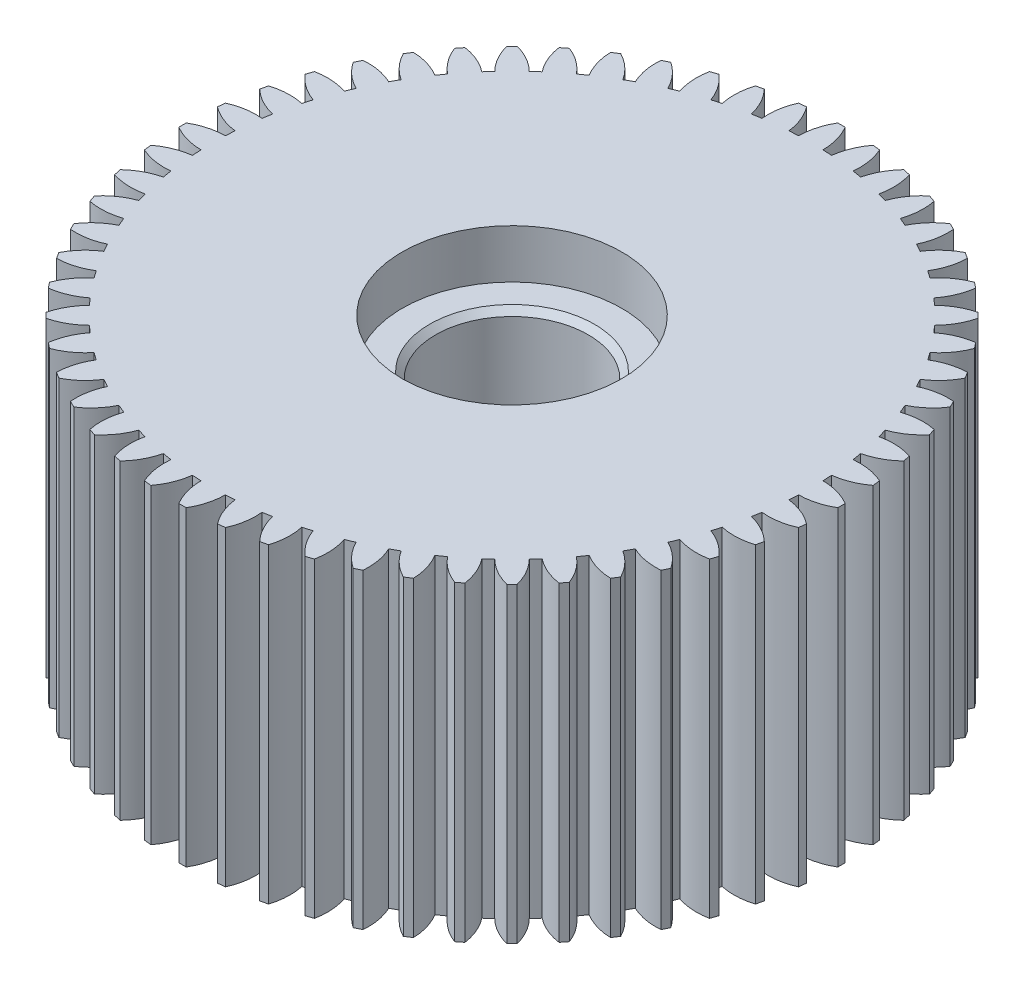
SolidWorks part; units mm, degrees
ref_plane "Front Plane" through (0, 0, 0) normal (0, 0, 1) x (1, 0, 0)
ref_plane "Top Plane" through (0, 0, 0) normal (0, 1, 0) x (1, 0, 0)
ref_plane "Right Plane" through (0, 0, 0) normal (1, 0, 0) x (0, 0, -1)
sketch "Sketch2" plane through (0, 0, 0) normal (0, 1, 0) x (1, 0, 0)
  circle A0 centre (0, 0) radius 24.5
  dimension "D1" = 49
extrude "Boss-Extrude1" add sketch "Sketch2" along normal blind 25.5
sketch "Sketch3" plane through (0, 25.5, 0) normal (0, 1, 0) x (1, 0, 0)
  line L0 (0, 0) -> (0, 40.3365) construction
  line L1 (-0.3, 26.9983) -> (0.3, 26.9983)
  line L2 (2.7247, 26.8622) -> (3.321, 26.795)
  line L3 (5.7152, 26.3882) -> (6.3002, 26.2547)
  line L4 (8.6338, 25.5824) -> (9.2001, 25.3842)
  line L5 (11.4438, 24.4548) -> (11.9844, 24.1945)
  line L6 (14.11, 23.0198) -> (14.618, 22.7005)
  line L7 (16.5986, 21.2952) -> (17.0677, 20.9211)
  line L8 (18.8786, 19.3028) -> (19.3028, 18.8786)
  line L9 (20.9211, 17.0677) -> (21.2952, 16.5986)
  line L10 (22.7005, 14.618) -> (23.0198, 14.11)
  line L11 (24.1945, 11.9844) -> (24.4548, 11.4438)
  line L12 (25.3842, 9.2001) -> (25.5824, 8.6338)
  line L13 (26.2547, 6.3002) -> (26.3882, 5.7152)
  line L14 (26.795, 3.321) -> (26.8622, 2.7247)
  line L15 (26.9983, 0.3) -> (26.9983, -0.3)
  line L16 (26.8622, -2.7247) -> (26.795, -3.321)
  line L17 (26.3882, -5.7152) -> (26.2547, -6.3002)
  line L18 (25.5824, -8.6338) -> (25.3842, -9.2001)
  line L19 (24.4548, -11.4438) -> (24.1945, -11.9844)
  line L20 (23.0198, -14.11) -> (22.7005, -14.618)
  line L21 (21.2952, -16.5986) -> (20.9211, -17.0677)
  line L22 (19.3028, -18.8786) -> (18.8786, -19.3028)
  line L23 (17.0677, -20.9211) -> (16.5986, -21.2952)
  line L24 (14.618, -22.7005) -> (14.11, -23.0198)
  line L25 (11.9844, -24.1945) -> (11.4438, -24.4548)
  line L26 (9.2001, -25.3842) -> (8.6338, -25.5824)
  line L27 (6.3002, -26.2547) -> (5.7152, -26.3882)
  line L28 (3.321, -26.795) -> (2.7247, -26.8622)
  line L29 (0.3, -26.9983) -> (-0.3, -26.9983)
  line L30 (-2.7247, -26.8622) -> (-3.321, -26.795)
  line L31 (-5.7152, -26.3882) -> (-6.3002, -26.2547)
  line L32 (-8.6338, -25.5824) -> (-9.2001, -25.3842)
  line L33 (-11.4438, -24.4548) -> (-11.9844, -24.1945)
  line L34 (-14.11, -23.0198) -> (-14.618, -22.7005)
  line L35 (-16.5986, -21.2952) -> (-17.0677, -20.9211)
  line L36 (-18.8786, -19.3028) -> (-19.3028, -18.8786)
  line L37 (-20.9211, -17.0677) -> (-21.2952, -16.5986)
  line L38 (-22.7005, -14.618) -> (-23.0198, -14.11)
  line L39 (-24.1945, -11.9844) -> (-24.4548, -11.4438)
  line L40 (-25.3842, -9.2001) -> (-25.5824, -8.6338)
  line L41 (-26.2547, -6.3002) -> (-26.3882, -5.7152)
  line L42 (-26.795, -3.321) -> (-26.8622, -2.7247)
  line L43 (-26.9983, -0.3) -> (-26.9983, 0.3)
  line L44 (-26.8622, 2.7247) -> (-26.795, 3.321)
  line L45 (-26.3882, 5.7152) -> (-26.2547, 6.3002)
  line L46 (-25.5824, 8.6338) -> (-25.3842, 9.2001)
  line L47 (-24.4548, 11.4438) -> (-24.1945, 11.9844)
  line L48 (-23.0198, 14.11) -> (-22.7005, 14.618)
  line L49 (-21.2952, 16.5986) -> (-20.9211, 17.0677)
  line L50 (-19.3028, 18.8786) -> (-18.8786, 19.3028)
  line L51 (-17.0677, 20.9211) -> (-16.5986, 21.2952)
  line L52 (-14.618, 22.7005) -> (-14.11, 23.0198)
  line L53 (-11.9844, 24.1945) -> (-11.4438, 24.4548)
  line L54 (-9.2001, 25.3842) -> (-8.6338, 25.5824)
  line L55 (-6.3002, 26.2547) -> (-5.7152, 26.3882)
  line L56 (-3.321, 26.795) -> (-2.7247, 26.8622)
  circle A0 centre (0, 0) radius 24.5 construction
  circle A1 centre (0, 0) radius 24.5
  circle A2 centre (0, 0) radius 27
  arc A3 (-1, 24.4796) -> (-0.3, 26.9983) centre (3.9999, 24.4467) cw
  arc A4 (1, 24.4796) -> (0.3, 26.9983) centre (-3.9999, 24.4467) ccw
  arc A5 (1.7471, 24.4376) -> (2.7247, 26.8622) centre (6.7119, 23.8451) cw
  arc A6 (3.7346, 24.2137) -> (3.321, 26.795) centre (-1.2376, 24.7408) ccw
  arc A7 (4.4723, 24.0884) -> (5.7152, 26.3882) centre (9.3395, 22.9437) cw
  arc A8 (6.4221, 23.6433) -> (6.3002, 26.2547) centre (1.5403, 24.7238) ccw
  arc A9 (7.1412, 23.4361) -> (8.6338, 25.5824) centre (11.8497, 21.7537) cw
  arc A10 (9.029, 22.7756) -> (9.2001, 25.3842) centre (4.2988, 24.3959) ccw
  arc A11 (9.7203, 22.4892) -> (11.4438, 24.4548) centre (14.2108, 20.2902) cw
  arc A12 (11.5223, 21.6215) -> (11.9844, 24.1945) centre (7.0032, 23.7612) ccw
  arc A13 (12.1772, 21.2595) -> (14.11, 23.0198) centre (16.3932, 18.5715) cw
  arc A14 (13.8706, 20.1954) -> (14.618, 22.7005) centre (9.6196, 22.8277) ccw
  arc A15 (14.4809, 19.7624) -> (16.5986, 21.2952) centre (18.3695, 16.6193) cw
  arc A16 (16.0446, 18.5154) -> (17.0677, 20.9211) centre (12.115, 21.6071) ccw
  arc A17 (16.6026, 18.0168) -> (18.8786, 19.3028) centre (20.1148, 14.4581) cw
  arc A18 (18.0168, 16.6026) -> (19.3028, 18.8786) centre (14.4581, 20.1148) ccw
  arc A19 (18.5154, 16.0446) -> (20.9211, 17.0677) centre (21.6071, 12.115) cw
  arc A20 (19.7624, 14.4809) -> (21.2952, 16.5986) centre (16.6193, 18.3695) ccw
  arc A21 (20.1954, 13.8706) -> (22.7005, 14.618) centre (22.8277, 9.6196) cw
  arc A22 (21.2595, 12.1772) -> (23.0198, 14.11) centre (18.5715, 16.3932) ccw
  arc A23 (21.6215, 11.5223) -> (24.1945, 11.9844) centre (23.7612, 7.0032) cw
  arc A24 (22.4892, 9.7203) -> (24.4548, 11.4438) centre (20.2902, 14.2108) ccw
  arc A25 (22.7756, 9.029) -> (25.3842, 9.2001) centre (24.3959, 4.2988) cw
  arc A26 (23.4361, 7.1412) -> (25.5824, 8.6338) centre (21.7537, 11.8497) ccw
  arc A27 (23.6433, 6.4221) -> (26.2547, 6.3002) centre (24.7238, 1.5403) cw
  arc A28 (24.0884, 4.4723) -> (26.3882, 5.7152) centre (22.9437, 9.3395) ccw
  arc A29 (24.2137, 3.7346) -> (26.795, 3.321) centre (24.7408, -1.2376) cw
  arc A30 (24.4376, 1.7471) -> (26.8622, 2.7247) centre (23.8451, 6.7119) ccw
  arc A31 (24.4796, 1) -> (26.9983, 0.3) centre (24.4467, -3.9999) cw
  arc A32 (24.4796, -1) -> (26.9983, -0.3) centre (24.4467, 3.9999) ccw
  arc A33 (24.4376, -1.7471) -> (26.8622, -2.7247) centre (23.8451, -6.7119) cw
  arc A34 (24.2137, -3.7346) -> (26.795, -3.321) centre (24.7408, 1.2376) ccw
  arc A35 (24.0884, -4.4723) -> (26.3882, -5.7152) centre (22.9437, -9.3395) cw
  arc A36 (23.6433, -6.4221) -> (26.2547, -6.3002) centre (24.7238, -1.5403) ccw
  arc A37 (23.4361, -7.1412) -> (25.5824, -8.6338) centre (21.7537, -11.8497) cw
  arc A38 (22.7756, -9.029) -> (25.3842, -9.2001) centre (24.3959, -4.2988) ccw
  arc A39 (22.4892, -9.7203) -> (24.4548, -11.4438) centre (20.2902, -14.2108) cw
  arc A40 (21.6215, -11.5223) -> (24.1945, -11.9844) centre (23.7612, -7.0032) ccw
  arc A41 (21.2595, -12.1772) -> (23.0198, -14.11) centre (18.5715, -16.3932) cw
  arc A42 (20.1954, -13.8706) -> (22.7005, -14.618) centre (22.8277, -9.6196) ccw
  arc A43 (19.7624, -14.4809) -> (21.2952, -16.5986) centre (16.6193, -18.3695) cw
  arc A44 (18.5154, -16.0446) -> (20.9211, -17.0677) centre (21.6071, -12.115) ccw
  arc A45 (18.0168, -16.6026) -> (19.3028, -18.8786) centre (14.4581, -20.1148) cw
  arc A46 (16.6026, -18.0168) -> (18.8786, -19.3028) centre (20.1148, -14.4581) ccw
  arc A47 (16.0446, -18.5154) -> (17.0677, -20.9211) centre (12.115, -21.6071) cw
  arc A48 (14.4809, -19.7624) -> (16.5986, -21.2952) centre (18.3695, -16.6193) ccw
  arc A49 (13.8706, -20.1954) -> (14.618, -22.7005) centre (9.6196, -22.8277) cw
  arc A50 (12.1772, -21.2595) -> (14.11, -23.0198) centre (16.3932, -18.5715) ccw
  arc A51 (11.5223, -21.6215) -> (11.9844, -24.1945) centre (7.0032, -23.7612) cw
  arc A52 (9.7203, -22.4892) -> (11.4438, -24.4548) centre (14.2108, -20.2902) ccw
  arc A53 (9.029, -22.7756) -> (9.2001, -25.3842) centre (4.2988, -24.3959) cw
  arc A54 (7.1412, -23.4361) -> (8.6338, -25.5824) centre (11.8497, -21.7537) ccw
  arc A55 (6.4221, -23.6433) -> (6.3002, -26.2547) centre (1.5403, -24.7238) cw
  arc A56 (4.4723, -24.0884) -> (5.7152, -26.3882) centre (9.3395, -22.9437) ccw
  arc A57 (3.7346, -24.2137) -> (3.321, -26.795) centre (-1.2376, -24.7408) cw
  arc A58 (1.7471, -24.4376) -> (2.7247, -26.8622) centre (6.7119, -23.8451) ccw
  arc A59 (1, -24.4796) -> (0.3, -26.9983) centre (-3.9999, -24.4467) cw
  arc A60 (-1, -24.4796) -> (-0.3, -26.9983) centre (3.9999, -24.4467) ccw
  arc A61 (-1.7471, -24.4376) -> (-2.7247, -26.8622) centre (-6.7119, -23.8451) cw
  arc A62 (-3.7346, -24.2137) -> (-3.321, -26.795) centre (1.2376, -24.7408) ccw
  arc A63 (-4.4723, -24.0884) -> (-5.7152, -26.3882) centre (-9.3395, -22.9437) cw
  arc A64 (-6.4221, -23.6433) -> (-6.3002, -26.2547) centre (-1.5403, -24.7238) ccw
  arc A65 (-7.1412, -23.4361) -> (-8.6338, -25.5824) centre (-11.8497, -21.7537) cw
  arc A66 (-9.029, -22.7756) -> (-9.2001, -25.3842) centre (-4.2988, -24.3959) ccw
  arc A67 (-9.7203, -22.4892) -> (-11.4438, -24.4548) centre (-14.2108, -20.2902) cw
  arc A68 (-11.5223, -21.6215) -> (-11.9844, -24.1945) centre (-7.0032, -23.7612) ccw
  arc A69 (-12.1772, -21.2595) -> (-14.11, -23.0198) centre (-16.3932, -18.5715) cw
  arc A70 (-13.8706, -20.1954) -> (-14.618, -22.7005) centre (-9.6196, -22.8277) ccw
  arc A71 (-14.4809, -19.7624) -> (-16.5986, -21.2952) centre (-18.3695, -16.6193) cw
  arc A72 (-16.0446, -18.5154) -> (-17.0677, -20.9211) centre (-12.115, -21.6071) ccw
  arc A73 (-16.6026, -18.0168) -> (-18.8786, -19.3028) centre (-20.1148, -14.4581) cw
  arc A74 (-18.0168, -16.6026) -> (-19.3028, -18.8786) centre (-14.4581, -20.1148) ccw
  arc A75 (-18.5154, -16.0446) -> (-20.9211, -17.0677) centre (-21.6071, -12.115) cw
  arc A76 (-19.7624, -14.4809) -> (-21.2952, -16.5986) centre (-16.6193, -18.3695) ccw
  arc A77 (-20.1954, -13.8706) -> (-22.7005, -14.618) centre (-22.8277, -9.6196) cw
  arc A78 (-21.2595, -12.1772) -> (-23.0198, -14.11) centre (-18.5715, -16.3932) ccw
  arc A79 (-21.6215, -11.5223) -> (-24.1945, -11.9844) centre (-23.7612, -7.0032) cw
  arc A80 (-22.4892, -9.7203) -> (-24.4548, -11.4438) centre (-20.2902, -14.2108) ccw
  arc A81 (-22.7756, -9.029) -> (-25.3842, -9.2001) centre (-24.3959, -4.2988) cw
  arc A82 (-23.4361, -7.1412) -> (-25.5824, -8.6338) centre (-21.7537, -11.8497) ccw
  arc A83 (-23.6433, -6.4221) -> (-26.2547, -6.3002) centre (-24.7238, -1.5403) cw
  arc A84 (-24.0884, -4.4723) -> (-26.3882, -5.7152) centre (-22.9437, -9.3395) ccw
  arc A85 (-24.2137, -3.7346) -> (-26.795, -3.321) centre (-24.7408, 1.2376) cw
  arc A86 (-24.4376, -1.7471) -> (-26.8622, -2.7247) centre (-23.8451, -6.7119) ccw
  arc A87 (-24.4796, -1) -> (-26.9983, -0.3) centre (-24.4467, 3.9999) cw
  arc A88 (-24.4796, 1) -> (-26.9983, 0.3) centre (-24.4467, -3.9999) ccw
  arc A89 (-24.4376, 1.7471) -> (-26.8622, 2.7247) centre (-23.8451, 6.7119) cw
  arc A90 (-24.2137, 3.7346) -> (-26.795, 3.321) centre (-24.7408, -1.2376) ccw
  arc A91 (-24.0884, 4.4723) -> (-26.3882, 5.7152) centre (-22.9437, 9.3395) cw
  arc A92 (-23.6433, 6.4221) -> (-26.2547, 6.3002) centre (-24.7238, 1.5403) ccw
  arc A93 (-23.4361, 7.1412) -> (-25.5824, 8.6338) centre (-21.7537, 11.8497) cw
  arc A94 (-22.7756, 9.029) -> (-25.3842, 9.2001) centre (-24.3959, 4.2988) ccw
  arc A95 (-22.4892, 9.7203) -> (-24.4548, 11.4438) centre (-20.2902, 14.2108) cw
  arc A96 (-21.6215, 11.5223) -> (-24.1945, 11.9844) centre (-23.7612, 7.0032) ccw
  arc A97 (-21.2595, 12.1772) -> (-23.0198, 14.11) centre (-18.5715, 16.3932) cw
  arc A98 (-20.1954, 13.8706) -> (-22.7005, 14.618) centre (-22.8277, 9.6196) ccw
  arc A99 (-19.7624, 14.4809) -> (-21.2952, 16.5986) centre (-16.6193, 18.3695) cw
  arc A100 (-18.5154, 16.0446) -> (-20.9211, 17.0677) centre (-21.6071, 12.115) ccw
  arc A101 (-18.0168, 16.6026) -> (-19.3028, 18.8786) centre (-14.4581, 20.1148) cw
  arc A102 (-16.6026, 18.0168) -> (-18.8786, 19.3028) centre (-20.1148, 14.4581) ccw
  arc A103 (-16.0446, 18.5154) -> (-17.0677, 20.9211) centre (-12.115, 21.6071) cw
  arc A104 (-14.4809, 19.7624) -> (-16.5986, 21.2952) centre (-18.3695, 16.6193) ccw
  arc A105 (-13.8706, 20.1954) -> (-14.618, 22.7005) centre (-9.6196, 22.8277) cw
  arc A106 (-12.1772, 21.2595) -> (-14.11, 23.0198) centre (-16.3932, 18.5715) ccw
  arc A107 (-11.5223, 21.6215) -> (-11.9844, 24.1945) centre (-7.0032, 23.7612) cw
  arc A108 (-9.7203, 22.4892) -> (-11.4438, 24.4548) centre (-14.2108, 20.2902) ccw
  arc A109 (-9.029, 22.7756) -> (-9.2001, 25.3842) centre (-4.2988, 24.3959) cw
  arc A110 (-7.1412, 23.4361) -> (-8.6338, 25.5824) centre (-11.8497, 21.7537) ccw
  arc A111 (-6.4221, 23.6433) -> (-6.3002, 26.2547) centre (-1.5403, 24.7238) cw
  arc A112 (-4.4723, 24.0884) -> (-5.7152, 26.3882) centre (-9.3395, 22.9437) ccw
  arc A113 (-3.7346, 24.2137) -> (-3.321, 26.795) centre (1.2376, 24.7408) cw
  arc A114 (-1.7471, 24.4376) -> (-2.7247, 26.8622) centre (-6.7119, 23.8451) ccw
  point P344 (0, 0)
  circle M172 centre (0, 0) radius 24.5
  dimension "D1" = 54
  dimension "D4" = 5
  dimension "D2" = 1
  dimension "D3" = 0.3
  dimension "D5" = 56
extrude "Boss-Extrude2" add sketch "Sketch3" against normal blind 25.5 contours L0 L1 A3 M172 | L0 A1 A4 L1 | A1 A6 L2 A5 | A1 A8 L3 A7 | A1 A10 L4 A9 | A1 A12 L5 A11 | A1 A14 L6 A13 | A1 A16 L7 A15 | A1 A18 L8 A17 | A1 A20 L9 A19 | A1 A22 L10 A21 | A1 A24 L11 A23 | A1 A26 L12 A25 | A1 A28 L13 A27 | A1 A30 L14 A29 | A1 A32 L15 A31 | A1 A34 L16 A33 | A1 A36 L17 A35 | A1 A38 L18 A37 | A1 A40 L19 A39 | A1 A42 L20 A41 | A1 A44 L21 A43 | A1 A46 L22 A45 | A1 A48 L23 A47 | A1 A50 L24 A49 | A1 A52 L25 A51 | A1 A54 L26 A53 | A1 A56 L27 A55 | A1 A58 L28 A57 | A1 A60 L29 A59 | A1 A62 L30 A61 | A1 A64 L31 A63 | A1 A66 L32 A65 | A1 A68 L33 A67 | A1 A70 L34 A69 | A1 A72 L35 A71 | A1 A74 L36 A73 | A1 A76 L37 A75 | A1 A78 L38 A77 | A1 A80 L39 A79 | A1 A114 L56 A113 | A1 A112 L55 A111 | A1 A110 L54 A109 | A1 A108 L53 A107 | A1 A106 L52 A105 | A1 A104 L51 A103 | A1 A102 L50 A101 | A1 A100 L49 A99 | A1 A98 L48 A97 | A1 A96 L47 A95 | A1 A94 L46 A93 | A1 A92 L45 A91 | A1 A90 L44 A89 | A1 A88 L43 A87 | A1 A86 L42 A85 | A1 A84 L41 A83 | A1 A82 L40 A81
sketch "Sketch4" plane through (0, 25.5, 0) normal (0, 1, 0) x (1, 0, 0)
  circle A0 centre (0, 0) radius 9
  dimension "D1" = 18
extrude "Cut-Extrude1" cut sketch "Sketch4" against normal blind 4
sketch "Sketch5" plane through (0, 21.5, 0) normal (0, 1, 0) x (1, 0, 0)
  circle A0 centre (0, 0) radius 6.25
  dimension "D1" = 12.5
extrude "Cut-Extrude3" cut sketch "Sketch5" against normal blind 30
chamfer "Chamfer1" distance 0.5 angle 45 1 edges at (0, 21.5, 6.25)
